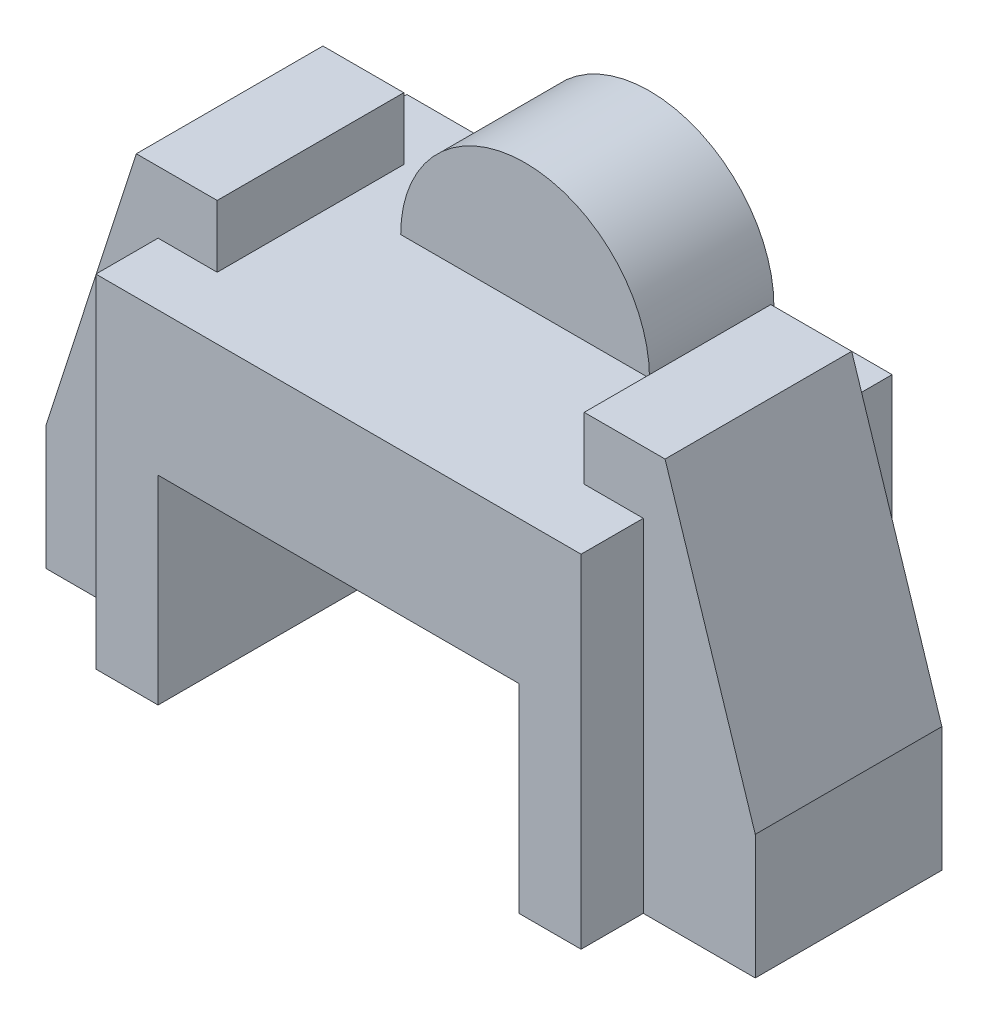
SolidWorks part; units mm, degrees
ref_plane "Front Plane" through (0, 0, 0) normal (0, 0, 1) x (1, 0, 0)
ref_plane "Top Plane" through (0, 0, 0) normal (0, 1, 0) x (1, 0, 0)
ref_plane "Right Plane" through (0, 0, 0) normal (1, 0, 0) x (0, 0, -1)
sketch "Sketch15" plane through (0, 0, 0) normal (0, 0, 1) x (1, 0, 0)
  line L1 (0, 0) -> (78, 0)
  line L2 (0, 0) -> (0, 55)
  line L3 (0, 55) -> (78, 55)
  line L4 (78, 0) -> (78, 55)
  dimension "D1" = 78
  dimension "D2" = 55
extrude "Boss-Extrude9" add sketch "Sketch15" along normal blind 50
sketch "Sketch16" plane through (0, 0, 50) normal (0, 0, 1) x (1, 0, 0)
  line L0 (0, 0) -> (78, 0) construction
  line L1 (10, 0) -> (68, 0)
  line L2 (10, 0) -> (10, 32)
  line L3 (10, 32) -> (68, 32)
  line L4 (68, 0) -> (68, 32)
  line L5 (0, 55) -> (0, 0) construction
  line L6 (78, 0) -> (78, 55) construction
  dimension "D1" = 10
  dimension "D2" = 10
  dimension "D3" = 32
extrude "Cut-Extrude3" cut sketch "Sketch16" against normal blind 50
sketch "Sketch17" plane through (0, 0, 0) normal (0, 0, -1) x (-1, 0, 0)
  line L0 (-78, 55) -> (0, 55) construction
  circle A0 centre (-39, 55) radius 20
  dimension "D1" = 40
extrude "Boss-Extrude10" add sketch "Sketch17" against normal blind 20
ref_plane "Plane19" through (39, 0, 0) normal (-1, 0, 0) x (0, 0, 1)
ref_plane "Plane20" through (0, 0, 25) normal (0, 0, -1) x (-1, 0, 0)
sketch "Sketch21" plane through (0, 0, 25) normal (0, 0, -1) x (-1, 0, 0)
  line L1 (-9.5, 0) -> (18, 0)
  line L2 (-9.5, 0) -> (-9.5, 65)
  line L3 (-9.5, 65) -> (3.5, 65)
  line L4 (3.5, 65) -> (18, 20)
  line L5 (18, 20) -> (18, 0)
  line L6 (0, 0) -> (-10, 0) construction
  line L7 (-39, 77.5102) -> (-39, -11.9658) construction
  line L8 (-39, -12.65) -> (-39, 12.65) construction
  point P7 (0, 0)
  dimension "D1" = 65
  dimension "D2" = 18
  dimension "D3" = 13
  dimension "D4" = 20
  dimension "D5" = 42.5
extrude "Boss-Extrude11" add sketch "Sketch21" along normal mid plane 30
mirror "Mirror4" about plane through (39, 0, 0) normal (-1, 0, 0) of "Boss-Extrude11"
